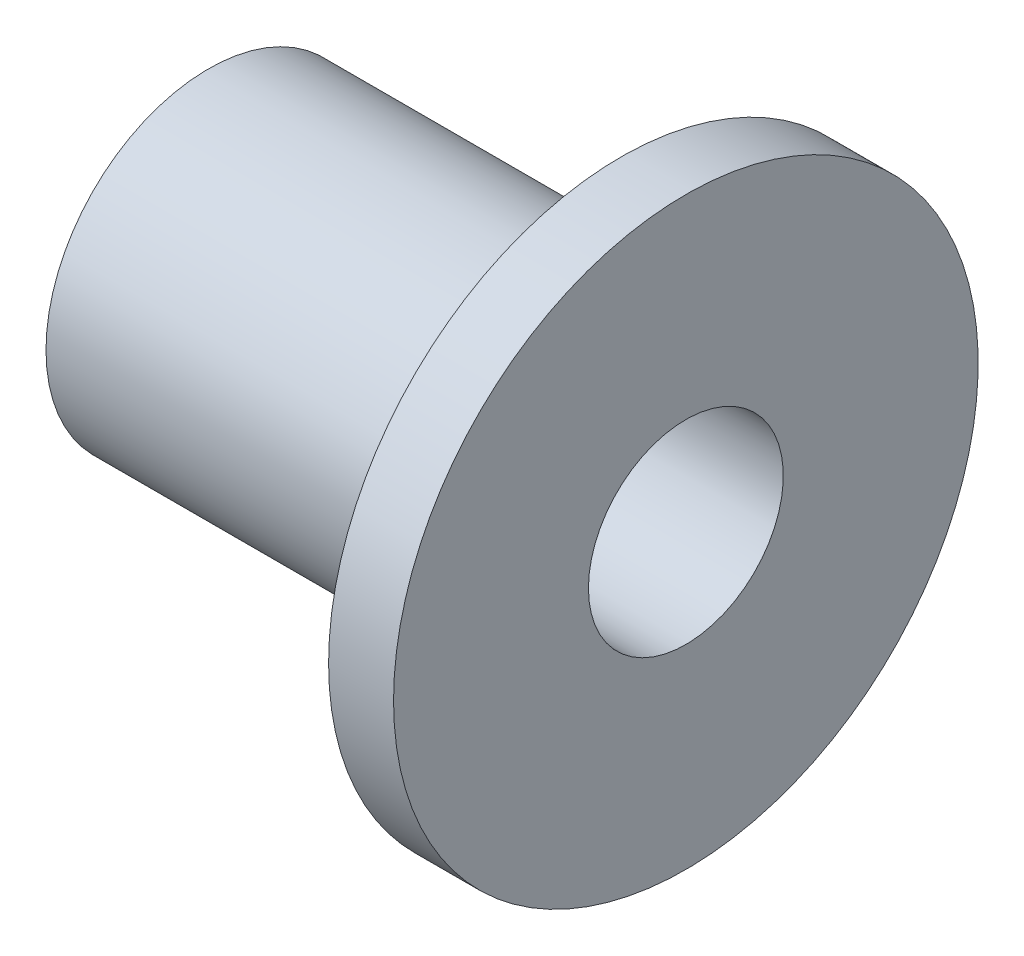
SolidWorks part; units mm, degrees
material "Nylon 101"
ref_plane "Front Plane" through (0, 0, 0) normal (0, 0, 1) x (1, 0, 0)
ref_plane "Top Plane" through (0, 0, 0) normal (0, 1, 0) x (1, 0, 0)
ref_plane "Right Plane" through (0, 0, 0) normal (1, 0, 0) x (0, 0, -1)
sketch "Sketch1" plane through (0, 0, 0) normal (0, 0, 1) x (1, 0, 0)
  line L0 (0, 0) -> (82.9832, 0) construction
  line L1 (0, 3) -> (14.7, 3)
  line L2 (14.7, 3) -> (14.7, 9)
  line L3 (14.7, 9) -> (12.7, 9)
  line L4 (12.7, 9) -> (12.7, 5)
  line L5 (12.7, 5) -> (0, 5)
  line L6 (0, 5) -> (0, 3)
  point P9 (0, 13.3623)
  dimension "D1" = 3
  dimension "D2" = 2
  dimension "D3" = 12.7
  dimension "D4" = 2
  dimension "D5" = 6
revolve "Revolve1" add sketch "Sketch1" angle 360 about L0
